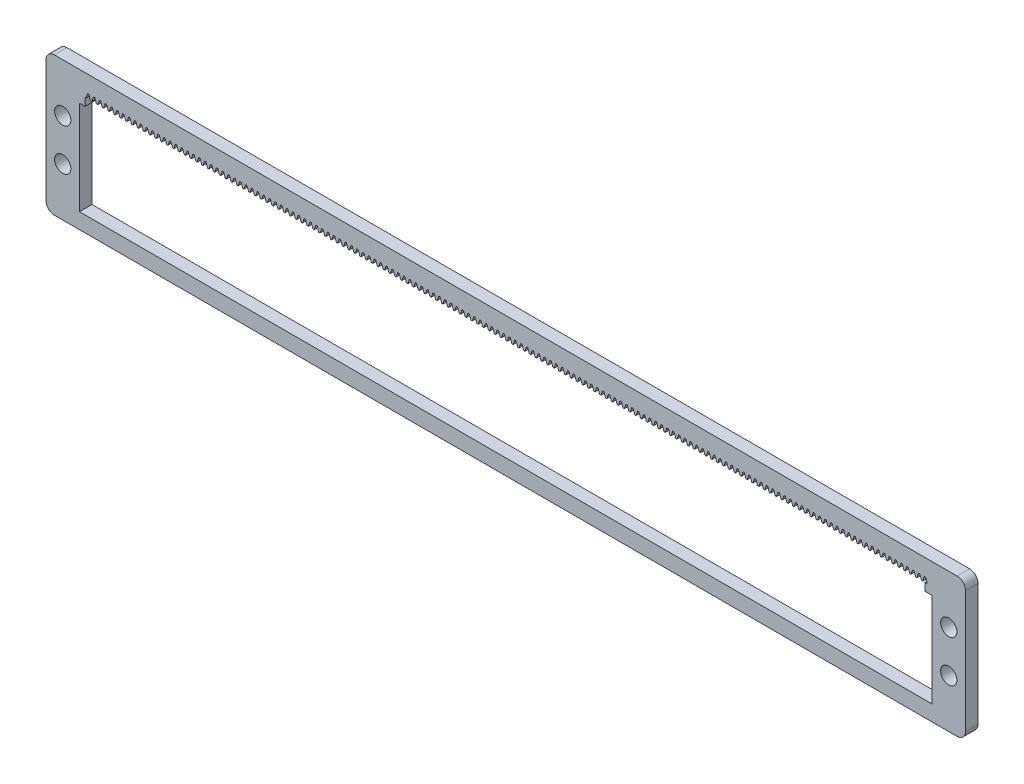
SolidWorks part; units mm, degrees
other "Markup1"
sketch "Sketch6" plane through (0, -30, 3.6) normal (0, 0, 1) x (1, 0, 0)
other "Markup2"
sketch "Sketch7" plane through (0, -30, 3.6) normal (0, 0, 1) x (1, 0, 0)
ref_plane "Front Plane" through (0, 0, 0) normal (0, 0, 1) x (1, 0, 0)
ref_plane "Top Plane" through (0, 0, 0) normal (0, 1, 0) x (1, 0, 0)
ref_plane "Right Plane" through (0, 0, 0) normal (1, 0, 0) x (0, 0, -1)
sketch "Sketch1" plane through (0, 0, 0) normal (0, 0, 1) x (1, 0, 0)
  line L1 (2, 0) -> (218, 0)
  line L2 (0, -2) -> (0, -31.22)
  line L3 (2, -33.22) -> (218, -33.22)
  line L4 (220, -2) -> (220, -31.22)
  arc A0 (218, -33.22) -> (220, -31.22) centre (218, -31.22) ccw
  arc A1 (0, -31.22) -> (2, -33.22) centre (2, -31.22) ccw
  arc A2 (2, 0) -> (0, -2) centre (2, -2) ccw
  arc A3 (218, 0) -> (220, -2) centre (218, -2) cw
  point P7 (220, -33.22)
  point P12 (0, 0)
  point P15 (220, 0)
  dimension "D3" = 2
  dimension "D1" = 33.22
  dimension "D2" = 220
extrude "Boss-Extrude1" add sketch "Sketch1" along normal blind 3
sketch "Sketch2" plane through (0, 0, 3) normal (0, 0, 1) x (1, 0, 0)
  line L0 (2, -33.22) -> (218, -33.22) construction
  line L1 (8, -7) -> (212, -7)
  line L2 (8, -7) -> (8, -29.5)
  line L3 (8, -29.5) -> (212, -29.5)
  line L4 (212, -7) -> (212, -29.5)
  line L5 (0, -2) -> (0, -31.22) construction
  line L7 (220, -31.22) -> (220, -2) construction
  line L8 (8, -18.25) -> (212, -18.25) construction
  line L12 (8, -29.5) -> (212, -29.5) construction
  line L13 (212, -4.3144) -> (212, -29.5) construction
  dimension "D1" = 22.5
  dimension "D2" = 8
  dimension "D3" = 8
  dimension "D4" = 3.72
extrude "Cut-Extrude1" cut sketch "Sketch2" against normal through all
sketch "Sketch3" plane through (0, 0, 3) normal (0, 0, 1) x (1, 0, 0)
  line L0 (212, -7) -> (8, -7) construction
  line L1 (9.35, -7) -> (210.32, -7)
  line L2 (9.35, -7) -> (9.35, -5.15)
  line L3 (9.35, -5.15) -> (210.32, -5.15)
  line L4 (210.32, -7) -> (210.32, -5.15)
  line L5 (212, -29.5) -> (212, -7) construction
  line L6 (8, -7) -> (8, -29.5) construction
  dimension "D1" = 1.85
  dimension "D2" = 1.68
  dimension "D3" = 1.35
extrude "Cut-Extrude2" cut sketch "Sketch3" against normal through all
sketch "Sketch4" plane through (0, 0, 3) normal (0, 0, 1) x (1, 0, 0)
  line L0 (211.345, -5.15) -> (210.865, -5.15) construction
  line L1 (210.32, -5.15) -> (9.35, -5.15) construction
  line L2 (211.345, -5.15) -> (211.725, -4.0118) construction
  line L3 (211.725, -4.0118) -> (210.485, -4.0118) construction
  line L4 (210.485, -4.0118) -> (210.865, -5.15)
  line L5 (210.485, -4.0118) -> (210.155, -4.0118)
  line L6 (210.155, -4.0118) -> (209.775, -5.15)
  line L7 (209.775, -5.15) -> (210.865, -5.15)
  line L10 (210.865, -5.15) -> (211.345, -5.15) construction
  dimension "D1" = 0.48
  dimension "D2" = 1.2
  dimension "D3" = 1.2
  dimension "D4" = 0.33
  dimension "D5" = 1.24
  dimension "D6" = 1.2
extrude "Cut-Extrude4" cut sketch "Sketch4" against normal through all
pattern_linear "LPattern1" count 144 spacing 1.4 along (-1, 0, 0) of "Cut-Extrude4"
sketch "Sketch5" plane through (0, 0, 3) normal (0, 0, 1) x (1, 0, 0)
  line L0 (212, -16.61) -> (220, -16.61) construction
  line L1 (218, 0) -> (2, 0) construction
  line L2 (8, -7) -> (8, -29.5) construction
  line L3 (0, -2) -> (0, -31.22) construction
  line L4 (2, -33.22) -> (218, -33.22) construction
  line L5 (0, -16.61) -> (8, -16.61) construction
  line L7 (216, -11.61) -> (216, -21.61) construction
  line L8 (4, -11.61) -> (4, -21.61) construction
  line L9 (212, -29.5) -> (212, -7) construction
  line L10 (220, -31.22) -> (220, -2) construction
  circle A4 centre (4, -11.61) radius 1.95
  circle A5 centre (4, -21.61) radius 1.95
  circle A6 centre (216, -11.61) radius 1.95
  circle A7 centre (216, -21.61) radius 1.95
  point P8 (216, -16.61)
  point P18 (4, -16.61)
  point P22 (4, -16.61)
  point P31 (216, -16.61)
  dimension "D1" = 3.9
  dimension "D3" = 3.9
  dimension "D4" = 3.9
  dimension "D6" = 3.9
  dimension "D5" = 10
  dimension "D7" = 10
extrude "Cut-Extrude5" cut sketch "Sketch5" against normal blind 10
